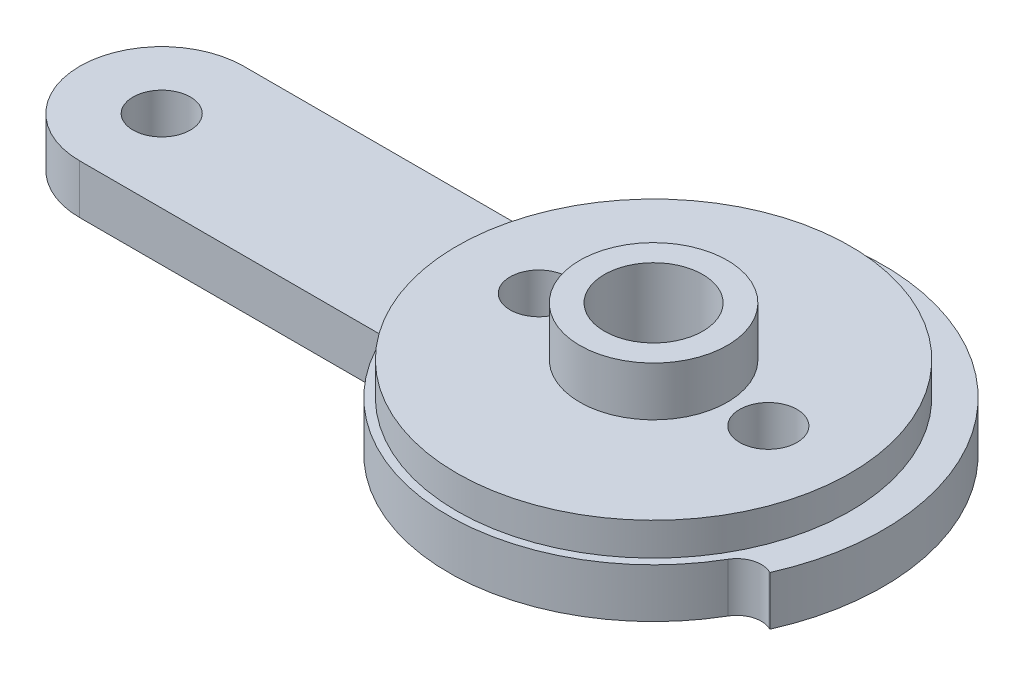
SolidWorks part; units mm, degrees
material "PET"
ref_plane "Спереди" through (0, 0, 0) normal (0, 0, 1) x (1, 0, 0)
ref_plane "Сверху" through (0, 0, 0) normal (0, 1, 0) x (1, 0, 0)
ref_plane "Справа" through (0, 0, 0) normal (1, 0, 0) x (0, 0, -1)
sketch "Эскиз1" plane through (0, 0, 0) normal (0, 1, 0) x (1, 0, 0)
  line L0 (0, 0) -> (-30, 0) construction
  line L1 (-30, 5) -> (-11.4564, 5)
  line L2 (-30, -5) -> (-11.4564, -5)
  line L4 (12.716, -5.6615) -> (12.7896, -5.6943)
  line L5 (-8.5696, 10.9686) -> (-8.6193, 11.0322)
  arc A0 (12.7896, -5.6943) -> (-8.6193, 11.0322) centre (0, 0) ccw
  arc A1 (-11.4564, -5) -> (10.8088, -6.2784) centre (0, 0) ccw
  arc A2 (-30, 5) -> (-30, -5) centre (-30, 0) ccw
  circle A3 centre (-30, 0) radius 1.75
  arc A4 (-8.7068, 8.9689) -> (-11.4564, 5) centre (0, 0) ccw
  arc A5 (10.8088, -6.2784) -> (12.716, -5.6615) centre (12.1059, -7.0319) cw
  arc A6 (-8.5696, 10.9686) -> (-8.7068, 8.9689) centre (-9.7517, 10.0452) cw
  point P13 (0, 0)
  point P16 (0, 0)
  point P18 (-7.6958, 9.8501)
  dimension "D1" = 28
  dimension "D2" = 25
  dimension "D3" = 10
  dimension "D5" = 3.5
  dimension "D6" = 1.5
  dimension "D7" = 1.5
  dimension "D4" = 30
extrude "Бобышка-Вытянуть1" add sketch "Эскиз1" along normal blind 3
sketch "Эскиз2" plane through (0, 3, 0) normal (0, 1, 0) x (1, 0, 0)
  circle A0 centre (0, 0) radius 12
  dimension "D1" = 24
extrude "Бобышка-Вытянуть2" add sketch "Эскиз2" along normal blind 2
sketch "Эскиз3" plane through (0, 5, 0) normal (0, 1, 0) x (1, 0, 0)
  circle A0 centre (0, 0) radius 4.5
  circle A1 centre (0, 0) radius 3
  dimension "D1" = 9
  dimension "D2" = 6
extrude "Бобышка-Вытянуть3" add sketch "Эскиз3" along normal blind 3
sketch "Эскиз4" plane through (0, 5, 0) normal (0, 1, 0) x (1, 0, 0)
  circle A0 centre (0, 0) radius 3
extrude "Вырез-Вытянуть1" cut sketch "Эскиз4" against normal blind 2
sketch "Эскиз5" plane through (0, 8, 0) normal (0, 1, 0) x (1, 0, 0)
  circle A0 centre (0, 0) radius 1.75
  circle A1 centre (-7, 0) radius 1.75
  circle A2 centre (7, 0) radius 1.75
  dimension "D1" = 3.5
  dimension "D2" = 3.5
  dimension "D3" = 3.5
  dimension "D4" = 7
  dimension "D5" = 7
extrude "Вырез-Вытянуть2" cut sketch "Эскиз5" against normal through all
